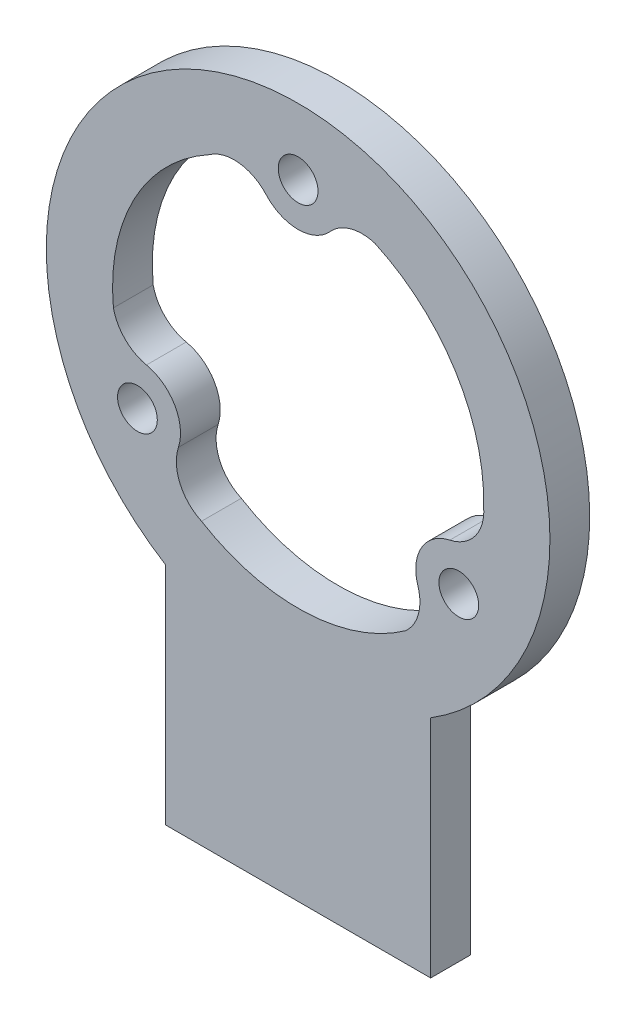
SolidWorks part; units mm, degrees
ref_plane "Plan de face" through (0, 0, 0) normal (0, 0, 1) x (1, 0, 0)
ref_plane "Plan de dessus" through (0, 0, 0) normal (0, 1, 0) x (1, 0, 0)
ref_plane "Plan de droite" through (0, 0, 0) normal (1, 0, 0) x (0, 0, -1)
sketch "Esquisse1" plane through (0, 0, 0) normal (0, 0, 1) x (1, 0, 0)
  line L0 (0, 14) -> (-12.125, -7.0011) construction
  line L1 (-12.125, -7.0011) -> (-10.6244, -7.0011) construction
  line L2 (12.125, -7.0011) -> (0, 14) construction
  line L5 (10, -16.1555) -> (10, -33.1555)
  line L6 (10, -33.1555) -> (-10, -33.1555)
  line L7 (-10, -16.1555) -> (-10, -33.1555)
  line L13 (10.6244, -7.0011) -> (12.125, -7.0011) construction
  arc A0 (10, -16.1555) -> (-10, -16.1555) centre (0, 0) ccw
  circle A2 centre (0, 14) radius 1.5
  arc A12 (-2.411, 11.8207) -> (2.411, 11.8207) centre (0, 14) ccw
  arc A16 (5.8094, 12.7378) -> (2.411, 11.8207) centre (4.8221, 9.6414) ccw
  arc A17 (-2.411, 11.8207) -> (-6.7074, 12.2887) centre (-4.8221, 9.6414) ccw
  arc A18 (-6.7074, 12.2887) -> (-13.9359, -1.3378) centre (0, 0) ccw
  arc A19 (8.1265, -11.4) -> (9.0315, -7.9984) centre (5.9386, -8.9967) ccw
  arc A20 (11.4425, -3.8223) -> (9.0315, -7.9984) centre (12.1244, -7) ccw
  arc A21 (11.4425, -3.8223) -> (13.996, -0.3356) centre (10.7607, -0.6447) ccw
  circle A22 centre (12.1244, -7) radius 1.5
  arc A23 (-13.9359, -1.3378) -> (-11.4425, -3.8223) centre (-10.7607, -0.6447) ccw
  arc A24 (-9.0315, -7.9984) -> (-11.4425, -3.8223) centre (-12.1244, -7) ccw
  arc A25 (-9.0315, -7.9984) -> (-7.2886, -11.9531) centre (-5.9386, -8.9967) ccw
  circle A26 centre (-12.1244, -7) radius 1.5
  arc A27 (-7.2886, -11.9531) -> (8.1265, -11.4) centre (0, 0) ccw
  arc A28 (13.996, -0.3356) -> (5.8094, 12.7378) centre (0, 0) ccw
  circle A29 centre (0, 14) radius 3.25 construction
  point P1 (0, 0)
  point P7 (0, 0)
  point P31 (0, 0)
  point P36 (0, 0)
  point P37 (0, 0)
  point P45 (5.9386, -12.6491)
  dimension "D1" = 38
  dimension "D2" = 3
  dimension "D3" = 3
  dimension "D4" = 6.5
  dimension "D5" = 14
  dimension "D8" = 14
  dimension "D9" = 3.25
  dimension "D10" = 14
  dimension "D11" = 3.25
  dimension "D12" = 24.25
  dimension "D13" = 24.25
  dimension "D16" = 20
  dimension "D6" = 60
  dimension "D7" = 60
  dimension "D14" = 10.78
  dimension "D15" = 10.78
  dimension "D17" = 17
  dimension "D18" = 17
extrude "Boss.-Extru.2" add sketch "Esquisse1" along normal blind 3
